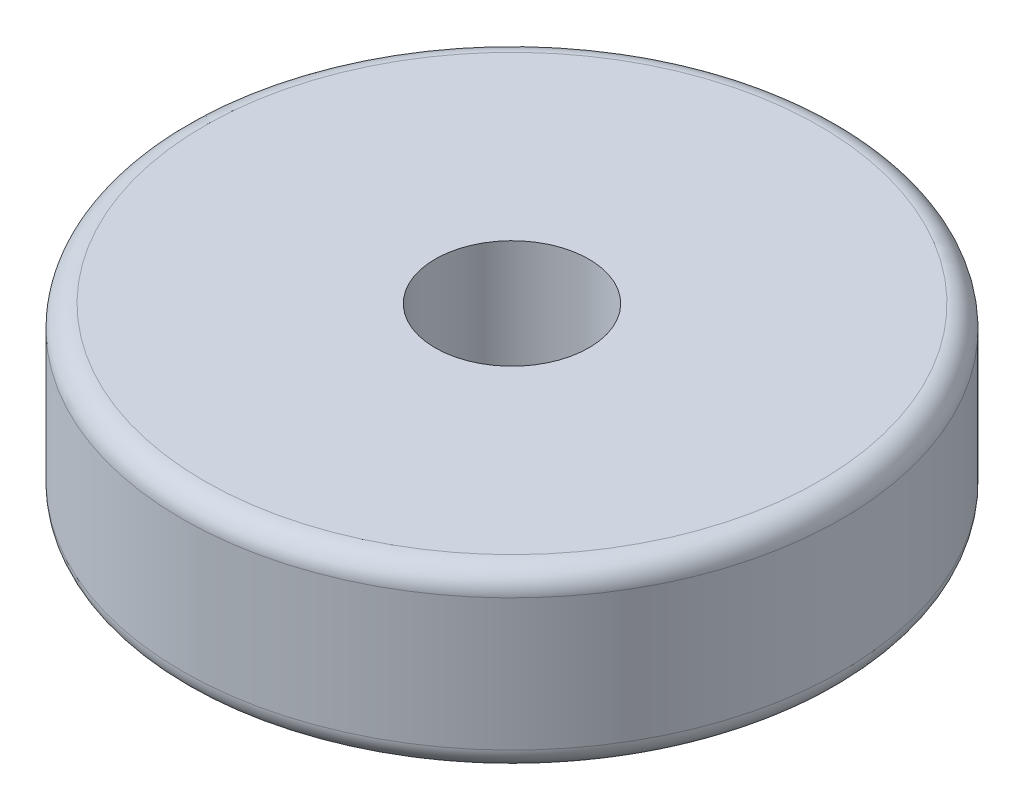
SolidWorks part; units mm, degrees
material "ABS"
ref_plane "Front Plane" through (0, 0, 0) normal (0, 0, 1) x (1, 0, 0)
ref_plane "Top Plane" through (0, 0, 0) normal (0, 1, 0) x (1, 0, 0)
ref_plane "Right Plane" through (0, 0, 0) normal (1, 0, 0) x (0, 0, -1)
sketch "Sketch1" plane through (0, 0, 0) normal (0, 1, 0) x (1, 0, 0)
  circle A0 centre (0, 0) radius 7.5
  dimension "D1" = 15
extrude "Boss-Extrude1" add sketch "Sketch1" along normal blind 4
sketch "Sketch2" plane through (0, 4, 0) normal (0, 1, 0) x (1, 0, 0)
  circle A0 centre (0, 0) radius 1.75
  dimension "D1" = 3.5
extrude "Cut-Extrude1" cut sketch "Sketch2" against normal blind 4
fillet "Fillet1" radius 0.5 2 edges at (0, 0, 7.5) (0, 4, 7.5)
